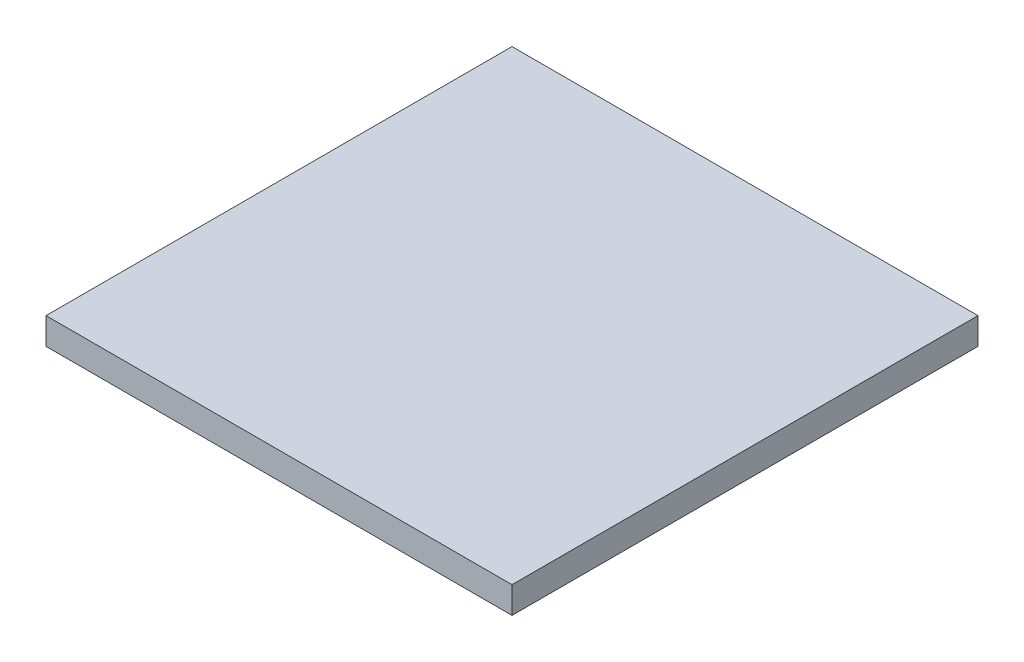
SolidWorks part; units mm, degrees
ref_plane "Front Plane" through (0, 0, 0) normal (0, 0, 1) x (1, 0, 0)
ref_plane "Top Plane" through (0, 0, 0) normal (0, 1, 0) x (1, 0, 0)
ref_plane "Right Plane" through (0, 0, 0) normal (1, 0, 0) x (0, 0, -1)
sketch "Sketch1" plane through (0, 0, 0) normal (0, 1, 0) x (1, 0, 0)
  line L1 (-192.9217, 110.1657) -> (157.0783, 110.1657)
  line L2 (-192.9217, 110.1657) -> (-192.9217, -239.8343)
  line L3 (-192.9217, -239.8343) -> (157.0783, -239.8343)
  line L4 (157.0783, 110.1657) -> (157.0783, -239.8343)
  dimension "D1" = 350
  dimension "D2" = 350
extrude "Boss-Extrude1" add sketch "Sketch1" along normal blind 20
